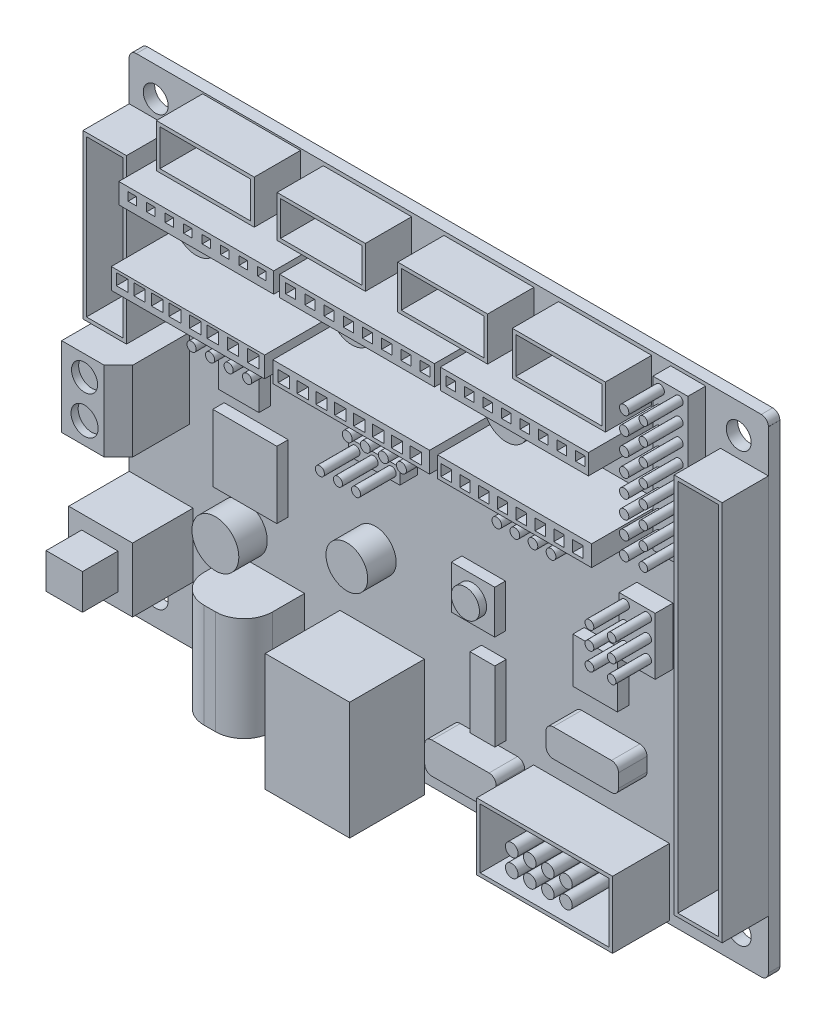
SolidWorks part; units mm, degrees
ref_plane "Plan de face" through (0, 0, 0) normal (0, 0, 1) x (1, 0, 0)
ref_plane "Plan de dessus" through (0, 0, 0) normal (0, 1, 0) x (1, 0, 0)
ref_plane "Plan de droite" through (0, 0, 0) normal (1, 0, 0) x (0, 0, -1)
sketch "Esquisse1" plane through (0, 0, 0) normal (0, 0, 1) x (1, 0, 0)
  line L0 (10.1605, 117.1315) -> (100.1605, 117.1315) construction
  line L1 (14.1823, 118.8222) -> (112.2388, 118.8222) construction
  line L2 (96.1036, 120.9113) -> (96.1036, 117.241) construction
  line L3 (14.1823, 118.8222) -> (14.1823, 52.8789) construction
  line L4 (14.1823, 58.5882) -> (96.1036, 58.5882) construction
  line L5 (17.4191, 122.975) -> (9.0854, 122.975) construction
  line L6 (10.4529, 118.3065) -> (10.4529, 124.6287) construction
  line L7 (100.2754, 62.2127) -> (100.2754, 51.8116) construction
  line L8 (93.0262, 54.5082) -> (103.9351, 54.5082) construction
  line L10 (99.2754, 54.5082) -> (11.4529, 54.5082)
  line L11 (100.2754, 55.5082) -> (100.2754, 121.975)
  line L12 (99.2754, 122.975) -> (11.4529, 122.975)
  line L13 (10.4529, 55.5082) -> (10.4529, 121.975)
  circle A0 centre (14.1823, 118.8222) radius 1.75
  circle A1 centre (96.1036, 118.8222) radius 1.75
  circle A2 centre (14.1823, 58.5882) radius 1.75
  circle A3 centre (96.1036, 58.5882) radius 1.75
  arc A4 (11.4529, 54.5082) -> (10.4529, 55.5082) centre (11.4529, 55.5082) cw
  arc A5 (99.2754, 54.5082) -> (100.2754, 55.5082) centre (99.2754, 55.5082) ccw
  arc A6 (100.2754, 121.975) -> (99.2754, 122.975) centre (99.2754, 121.975) ccw
  arc A7 (11.4529, 122.975) -> (10.4529, 121.975) centre (11.4529, 121.975) ccw
  point P30 (100.2754, 54.5082)
  point P35 (10.4529, 122.975)
  dimension "D2" = 3.5
  dimension "D3" = 1
  dimension "D1" = 90
sketch "usbplug" plane through (0, 0, 0) normal (0, 0, 1) x (1, 0, 0)
  line L1 (40.0653, 69.5241) -> (51.931, 69.5241)
  line L2 (40.0653, 69.5241) -> (40.0653, 52.9888)
  line L3 (40.0653, 52.9888) -> (51.931, 52.9888)
  line L4 (51.931, 69.5241) -> (51.931, 52.9888)
sketch "power12v" plane through (0, 0, 0) normal (0, 0, 1) x (1, 0, 0)
  line L0 (99.2754, 54.5082) -> (11.4529, 54.5082) construction
  line L1 (25.4676, 69.1019) -> (35.0978, 69.1019)
  line L2 (25.4676, 69.1019) -> (25.4676, 54.5082)
  line L3 (25.4676, 54.5082) -> (35.0978, 54.5082)
  line L4 (35.0978, 69.1019) -> (35.0978, 54.5082)
sketch "yellow females" plane through (0, 0, 0) normal (0, 0, 1) x (1, 0, 0)
  line L0 (10.4529, 55.5082) -> (10.4529, 121.975) construction
  line L1 (20.7708, 122.7288) -> (34.5297, 122.7288)
  line L2 (20.7708, 122.7288) -> (20.7708, 116.6246)
  line L3 (20.7708, 116.6246) -> (34.5297, 116.6246)
  line L4 (34.5297, 122.7288) -> (34.5297, 116.6246)
  line L5 (37.7295, 122.458) -> (50.1346, 122.458)
  line L6 (37.7295, 122.458) -> (37.7295, 116.6246)
  line L7 (37.7295, 116.6246) -> (50.1346, 116.6246)
  line L8 (50.1346, 122.458) -> (50.1346, 116.6246)
  line L9 (54.6881, 122.458) -> (67.3148, 122.458)
  line L10 (54.6881, 122.458) -> (54.6881, 116.3613)
  line L11 (54.6881, 116.3613) -> (67.3148, 116.3613)
  line L12 (67.3148, 122.458) -> (67.3148, 116.3613)
  line L13 (70.7848, 122.458) -> (83.8646, 122.458)
  line L14 (70.7848, 122.458) -> (70.7848, 116.3613)
  line L15 (70.7848, 116.3613) -> (83.8646, 116.3613)
  line L16 (83.8646, 122.458) -> (83.8646, 116.3613)
  line L17 (16.5724, 116.3613) -> (10.4529, 116.3613)
  line L18 (16.5724, 116.3613) -> (16.5724, 93.4197)
  line L19 (16.5724, 93.4197) -> (10.4529, 93.4197)
  line L20 (10.4529, 116.3613) -> (10.4529, 93.4197)
  line L21 (100.2754, 55.5082) -> (100.2754, 121.975) construction
  line L22 (100.2754, 115.984) -> (93.5394, 115.984)
  line L23 (100.2754, 115.984) -> (100.2754, 62.4145)
  line L24 (100.2754, 62.4145) -> (93.5394, 62.4145)
  line L25 (93.5394, 115.984) -> (93.5394, 62.4145)
sketch "blue connector" plane through (0, 0, 0) normal (0, 0, 1) x (1, 0, 0)
  line L1 (18.9435, 92.796) -> (10.9645, 92.796)
  line L2 (18.9435, 92.796) -> (18.9435, 81.6185)
  line L3 (18.9435, 81.6185) -> (10.9645, 81.6185)
  line L4 (10.9645, 92.796) -> (10.9645, 81.6185)
sketch "blackheaders" plane through (0, 0, 0) normal (0, 0, 1) x (1, 0, 0)
  line L1 (67.2811, 64.3182) -> (86.3744, 64.3182)
  line L2 (67.2811, 64.3182) -> (67.2811, 54.9334)
  line L3 (67.2811, 54.9334) -> (86.3744, 54.9334)
  line L4 (86.3744, 64.3182) -> (86.3744, 54.9334)
sketch "yellow males" plane through (0, 0, 0) normal (0, 0, 1) x (1, 0, 0)
  line L1 (86.5421, 122.5145) -> (91.457, 122.5145)
  line L2 (86.5421, 122.5145) -> (86.5421, 101.3571)
  line L3 (86.5421, 101.3571) -> (91.457, 101.3571)
  line L4 (91.457, 122.5145) -> (91.457, 101.3571)
  line L5 (81.7885, 93.8085) -> (86.8611, 93.8085)
  line L6 (81.7885, 93.8085) -> (81.7885, 85.7708)
  line L7 (81.7885, 85.7708) -> (86.8611, 85.7708)
  line L8 (86.8611, 93.8085) -> (86.8611, 85.7708)
  line L9 (25.6843, 99.9383) -> (35.7056, 99.9383)
  line L10 (25.6843, 99.9383) -> (25.6843, 97.555)
  line L11 (25.6843, 97.555) -> (35.7056, 97.555)
  line L12 (35.7056, 99.9383) -> (35.7056, 97.555)
  line L13 (47.4499, 99.9383) -> (57.2554, 99.9383)
  line L14 (47.4499, 99.9383) -> (47.4499, 97.555)
  line L15 (47.4499, 97.555) -> (57.2554, 97.555)
  line L16 (57.2554, 99.9383) -> (57.2554, 97.555)
  line L17 (68.6129, 99.9383) -> (78.5026, 99.9383)
  line L18 (68.6129, 99.9383) -> (68.6129, 97.555)
  line L19 (68.6129, 97.555) -> (78.5026, 97.555)
  line L20 (78.5026, 99.9383) -> (78.5026, 97.555)
  line L21 (43.7893, 93.6501) -> (50.9757, 93.6501)
  line L22 (43.7893, 93.6501) -> (43.7893, 91.4595)
  line L23 (43.7893, 91.4595) -> (50.9757, 91.4595)
  line L24 (50.9757, 93.6501) -> (50.9757, 91.4595)
sketch "capa-crystals" plane through (0, 0, 0) normal (0, 0, 1) x (1, 0, 0)
  line L1 (74.0299, 74.3373) -> (82.2137, 74.3373)
  line L2 (73.0299, 73.3373) -> (73.0299, 71.4305)
  line L3 (74.0299, 70.4305) -> (82.2137, 70.4305)
  line L4 (83.2137, 73.3373) -> (83.2137, 71.4305)
  line L5 (56.9766, 64.2091) -> (65.0123, 64.2091)
  line L6 (55.9766, 63.2091) -> (55.9766, 60.8023)
  line L7 (56.9766, 59.8023) -> (65.0123, 59.8023)
  line L8 (66.0123, 63.2091) -> (66.0123, 60.8023)
  circle A0 centre (23.8645, 109.7983) radius 3.1857
  circle A1 centre (45.7317, 109.7645) radius 3.1076
  circle A2 centre (67.4261, 108.8502) radius 3.1456
  circle A3 centre (45.0345, 79.3108) radius 2.9321
  circle A4 centre (26.5615, 72.8809) radius 3.2963
  arc A5 (56.9766, 64.2091) -> (55.9766, 63.2091) centre (56.9766, 63.2091) ccw
  arc A6 (55.9766, 60.8023) -> (56.9766, 59.8023) centre (56.9766, 60.8023) ccw
  arc A7 (65.0123, 59.8023) -> (66.0123, 60.8023) centre (65.0123, 60.8023) ccw
  arc A8 (65.0123, 64.2091) -> (66.0123, 63.2091) centre (65.0123, 63.2091) cw
  arc A9 (74.0299, 74.3373) -> (73.0299, 73.3373) centre (74.0299, 73.3373) ccw
  arc A10 (73.0299, 71.4305) -> (74.0299, 70.4305) centre (74.0299, 71.4305) ccw
  arc A11 (82.2137, 70.4305) -> (83.2137, 71.4305) centre (82.2137, 71.4305) ccw
  arc A12 (82.2137, 74.3373) -> (83.2137, 73.3373) centre (82.2137, 73.3373) cw
  dimension "D1" = 1
sketch "black smd" plane through (0, 0, 0) normal (0, 0, 1) x (1, 0, 0)
  line L1 (24.6181, 95.8453) -> (30.2856, 95.8453)
  line L2 (24.6181, 95.8453) -> (24.6181, 89.4922)
  line L3 (24.6181, 89.4922) -> (30.2856, 89.4922)
  line L4 (30.2856, 95.8453) -> (30.2856, 89.4922)
  line L5 (23.7954, 86.6584) -> (32.7994, 86.6584)
  line L6 (23.7954, 86.6584) -> (23.7954, 77.243)
  line L7 (23.7954, 77.243) -> (32.7994, 77.243)
  line L8 (32.7994, 86.6584) -> (32.7994, 77.243)
  line L9 (74.3918, 84.6016) -> (80.6535, 84.6016)
  line L10 (74.3918, 84.6016) -> (74.3918, 78.2485)
  line L11 (74.3918, 78.2485) -> (80.6535, 78.2485)
  line L12 (80.6535, 84.6016) -> (80.6535, 78.2485)
  line L13 (59.9487, 75.2319) -> (63.4224, 75.2319)
  line L14 (59.9487, 75.2319) -> (59.9487, 65.3595)
  line L15 (59.9487, 65.3595) -> (63.4224, 65.3595)
  line L16 (63.4224, 75.2319) -> (63.4224, 65.3595)
extrude "Boss.-Extru.2" add sketch "black smd" along normal blind 1.6
extrude "Boss.-Extru.3" add sketch "capa-crystals" along normal blind 4 separate body
extrude "Boss.-Extru.4" add sketch "yellow males" along normal blind 2.5 separate body
extrude "Boss.-Extru.5" add sketch "blackheaders" along normal blind 8 separate body
extrude "Boss.-Extru.6" add sketch "blue connector" along normal blind 10 separate body
extrude "Boss.-Extru.7" add sketch "yellow females" along normal blind 6.5 separate body
extrude "Boss.-Extru.8" add sketch "power12v" along normal blind 8.5 separate body
extrude "Boss.-Extru.9" add sketch "usbplug" along normal blind 10.5 separate body
sketch "button" plane through (0, 0, 0) normal (0, 0, 1) x (1, 0, 0)
  line L0 (10.4529, 55.5082) -> (10.4529, 121.975) construction
  line L1 (10.4529, 71.6421) -> (19.4201, 71.6421)
  line L2 (10.4529, 71.6421) -> (10.4529, 62.6357)
  line L3 (10.4529, 62.6357) -> (19.4201, 62.6357)
  line L4 (19.4201, 71.6421) -> (19.4201, 62.6357)
extrude "Boss.-Extru.10" add sketch "button" along normal blind 8.5 separate body
sketch "reset" plane through (0, 0, 0) normal (0, 0, 1) x (1, 0, 0)
  line L1 (57.21, 84.7172) -> (63.3186, 84.7172)
  line L2 (57.21, 84.7172) -> (57.21, 78.6371)
  line L3 (57.21, 78.6371) -> (63.3186, 78.6371)
  line L4 (63.3186, 84.7172) -> (63.3186, 78.6371)
extrude "Boss.-Extru.11" add sketch "reset" along normal blind 1.5 separate body
sketch "boutrouge" plane through (0, 0, 1.5) normal (0, 0, 1) x (1, 0, 0)
  circle A0 centre (60.1919, 81.7159) radius 1.9818
extrude "Boss.-Extru.12" add sketch "boutrouge" along normal blind 1
sketch "boutonon" plane through (0, 0, 8.5) normal (0, 0, 1) x (1, 0, 0)
  line L1 (12.2781, 69.6518) -> (17.3868, 69.6518)
  line L2 (12.2781, 69.6518) -> (12.2781, 64.69)
  line L3 (12.2781, 64.69) -> (17.3868, 64.69)
  line L4 (17.3868, 69.6518) -> (17.3868, 64.69)
extrude "Boss.-Extru.13" add sketch "boutonon" along normal blind 5
chamfer "Chanfrein1" distance 2 angle 45 1 edges at (18.9435, 87.2073, 10)
fillet "Congé1" radius 4 2 edges at (35.0978, 61.8051, 8.5) (25.4676, 61.8051, 8.5)
sketch "Esquisse14" plane through (0, 54.5082, 0) normal (0, -1, 0) x (1, 0, 0)
  circle A0 centre (30.3404, 4.6082) radius 2.8723
extrude "Enlèv. mat.-Extru.1" cut sketch "Esquisse14" against normal blind 10
sketch "Esquisse15" plane through (0, 52.9888, 0) normal (0, -1, 0) x (1, 0, 0)
  line L0 (43.6813, 8.0587) -> (48.2181, 8.0587)
  line L1 (48.2181, 8.0587) -> (50.5333, 6.3037)
  line L2 (50.5333, 6.3037) -> (50.5333, 1.7855)
  line L3 (50.5333, 1.7855) -> (41.6835, 1.7855)
  line L4 (41.6835, 1.7855) -> (41.6835, 6.3783)
  line L5 (41.6835, 6.3783) -> (43.6813, 8.0587)
  line L6 (43.6813, 6.3783) -> (48.2181, 6.3783)
  line L7 (48.2181, 6.3783) -> (48.2181, 3.5413)
  line L8 (48.2181, 3.5413) -> (43.6813, 3.5413)
  line L9 (43.6813, 3.5413) -> (43.6813, 6.3783)
extrude "Enlèv. mat.-Extru.2" cut sketch "Esquisse15" against normal blind 10
shell "Coque1" thickness 0.5
shell "Coque2" thickness 0.5
shell "Coque3" thickness 0.5
shell "Coque4" thickness 0.5
shell "Coque5" thickness 0.5
shell "Coque6" thickness 0.5
shell "Coque7" thickness 0.5
sketch "Esquisse16" plane through (0, 0, 10) normal (0, 0, 1) x (1, 0, 0)
  line L0 (14.1823, 118.8222) -> (14.1823, 52.8789) construction
  circle A0 centre (14.1823, 89.9453) radius 1.8322
  circle A1 centre (14.1823, 84.6571) radius 1.9022
extrude "Enlèv. mat.-Extru.3" cut sketch "Esquisse16" against normal blind 1
sketch "connectures jaunes" plane through (0, 0, 0) normal (0, 0, 1) x (1, 0, 0)
  line L0 (22.9016, 115.5914) -> (22.9016, 114.431)
  line L1 (18.9914, 116.1815) -> (40.7575, 116.1815)
  line L2 (18.9914, 116.1815) -> (18.9914, 113.3359)
  line L3 (18.9914, 113.3359) -> (40.7575, 113.3359)
  line L4 (40.7575, 116.1815) -> (40.7575, 113.3359)
  line L5 (41.5914, 113.3359) -> (63.3426, 113.3359)
  line L6 (41.5914, 113.3359) -> (41.5914, 116.1815)
  line L7 (41.5914, 116.1815) -> (63.3426, 116.1815)
  line L8 (63.3426, 113.3359) -> (63.3426, 116.1815)
  line L9 (64.1704, 116.1815) -> (84.9797, 116.1815)
  line L10 (64.1704, 116.1815) -> (64.1704, 113.3359)
  line L11 (64.1704, 113.3359) -> (84.9797, 113.3359)
  line L12 (84.9797, 116.1815) -> (84.9797, 113.3359)
  line L13 (20.3016, 115.5914) -> (21.4462, 115.5914)
  line L14 (20.3016, 115.5914) -> (20.3016, 114.431)
  line L15 (20.3016, 114.431) -> (21.4462, 114.431)
  line L16 (21.4462, 115.5914) -> (21.4462, 114.431)
  line L17 (22.9016, 115.5914) -> (24.0462, 115.5914)
  line L18 (24.0462, 115.5914) -> (24.0462, 114.431)
  line L19 (22.9016, 114.431) -> (24.0462, 114.431)
  line L20 (25.5016, 115.5914) -> (25.5016, 114.431)
  line L21 (25.5016, 115.5914) -> (26.6462, 115.5914)
  line L22 (26.6462, 115.5914) -> (26.6462, 114.431)
  line L23 (25.5016, 114.431) -> (26.6462, 114.431)
  line L24 (28.1016, 115.5914) -> (28.1016, 114.431)
  line L25 (28.1016, 115.5914) -> (29.2462, 115.5914)
  line L26 (29.2462, 115.5914) -> (29.2462, 114.431)
  line L27 (28.1016, 114.431) -> (29.2462, 114.431)
  line L28 (30.7016, 115.5914) -> (30.7016, 114.431)
  line L29 (30.7016, 115.5914) -> (31.8462, 115.5914)
  line L30 (31.8462, 115.5914) -> (31.8462, 114.431)
  line L31 (30.7016, 114.431) -> (31.8462, 114.431)
  line L32 (33.3016, 115.5914) -> (33.3016, 114.431)
  line L33 (33.3016, 115.5914) -> (34.4462, 115.5914)
  line L34 (34.4462, 115.5914) -> (34.4462, 114.431)
  line L35 (33.3016, 114.431) -> (34.4462, 114.431)
  line L36 (35.9016, 115.5914) -> (35.9016, 114.431)
  line L37 (35.9016, 115.5914) -> (37.0462, 115.5914)
  line L38 (37.0462, 115.5914) -> (37.0462, 114.431)
  line L39 (35.9016, 114.431) -> (37.0462, 114.431)
  line L40 (38.5016, 115.5914) -> (38.5016, 114.431)
  line L41 (38.5016, 115.5914) -> (39.6462, 115.5914)
  line L42 (39.6462, 115.5914) -> (39.6462, 114.431)
  line L43 (38.5016, 114.431) -> (39.6462, 114.431)
  line L44 (45.1347, 115.5914) -> (45.1347, 114.2232)
  line L45 (42.4347, 115.5914) -> (43.8469, 115.5914)
  line L46 (42.4347, 115.5914) -> (42.4347, 114.2232)
  line L47 (42.4347, 114.2232) -> (43.8469, 114.2232)
  line L48 (43.8469, 115.5914) -> (43.8469, 114.2232)
  line L49 (45.1347, 115.5914) -> (46.5469, 115.5914)
  line L50 (46.5469, 115.5914) -> (46.5469, 114.2232)
  line L51 (45.1347, 114.2232) -> (46.5469, 114.2232)
  line L52 (47.8347, 115.5914) -> (47.8347, 114.2232)
  line L53 (47.8347, 115.5914) -> (49.2469, 115.5914)
  line L54 (49.2469, 115.5914) -> (49.2469, 114.2232)
  line L55 (47.8347, 114.2232) -> (49.2469, 114.2232)
  line L56 (50.5347, 115.5914) -> (50.5347, 114.2232)
  line L57 (50.5347, 115.5914) -> (51.9469, 115.5914)
  line L58 (51.9469, 115.5914) -> (51.9469, 114.2232)
  line L59 (50.5347, 114.2232) -> (51.9469, 114.2232)
  line L60 (53.2347, 115.5914) -> (53.2347, 114.2232)
  line L61 (53.2347, 115.5914) -> (54.6469, 115.5914)
  line L62 (54.6469, 115.5914) -> (54.6469, 114.2232)
  line L63 (53.2347, 114.2232) -> (54.6469, 114.2232)
  line L64 (55.9347, 115.5914) -> (55.9347, 114.2232)
  line L65 (55.9347, 115.5914) -> (57.3469, 115.5914)
  line L66 (57.3469, 115.5914) -> (57.3469, 114.2232)
  line L67 (55.9347, 114.2232) -> (57.3469, 114.2232)
  line L68 (58.6347, 115.5914) -> (58.6347, 114.2232)
  line L69 (58.6347, 115.5914) -> (60.0469, 115.5914)
  line L70 (60.0469, 115.5914) -> (60.0469, 114.2232)
  line L71 (58.6347, 114.2232) -> (60.0469, 114.2232)
  line L72 (61.3347, 115.5914) -> (61.3347, 114.2232)
  line L73 (61.3347, 115.5914) -> (62.7469, 115.5914)
  line L74 (62.7469, 115.5914) -> (62.7469, 114.2232)
  line L75 (61.3347, 114.2232) -> (62.7469, 114.2232)
  line L76 (67.5787, 115.5346) -> (67.5787, 114.2232)
  line L77 (64.9787, 115.5346) -> (66.2841, 115.5346)
  line L78 (64.9787, 115.5346) -> (64.9787, 114.2232)
  line L79 (64.9787, 114.2232) -> (66.2841, 114.2232)
  line L80 (66.2841, 115.5346) -> (66.2841, 114.2232)
  line L81 (67.5787, 115.5346) -> (68.8841, 115.5346)
  line L82 (68.8841, 115.5346) -> (68.8841, 114.2232)
  line L83 (67.5787, 114.2232) -> (68.8841, 114.2232)
  line L84 (70.1787, 115.5346) -> (70.1787, 114.2232)
  line L85 (70.1787, 115.5346) -> (71.4841, 115.5346)
  line L86 (71.4841, 115.5346) -> (71.4841, 114.2232)
  line L87 (70.1787, 114.2232) -> (71.4841, 114.2232)
  line L88 (72.7787, 115.5346) -> (72.7787, 114.2232)
  line L89 (72.7787, 115.5346) -> (74.0841, 115.5346)
  line L90 (74.0841, 115.5346) -> (74.0841, 114.2232)
  line L91 (72.7787, 114.2232) -> (74.0841, 114.2232)
  line L92 (75.3787, 115.5346) -> (75.3787, 114.2232)
  line L93 (75.3787, 115.5346) -> (76.6841, 115.5346)
  line L94 (76.6841, 115.5346) -> (76.6841, 114.2232)
  line L95 (75.3787, 114.2232) -> (76.6841, 114.2232)
  line L96 (77.9787, 115.5346) -> (77.9787, 114.2232)
  line L97 (77.9787, 115.5346) -> (79.2841, 115.5346)
  line L98 (79.2841, 115.5346) -> (79.2841, 114.2232)
  line L99 (77.9787, 114.2232) -> (79.2841, 114.2232)
  line L100 (80.5787, 115.5346) -> (80.5787, 114.2232)
  line L101 (80.5787, 115.5346) -> (81.8841, 115.5346)
  line L102 (81.8841, 115.5346) -> (81.8841, 114.2232)
  line L103 (80.5787, 114.2232) -> (81.8841, 114.2232)
  line L104 (83.1787, 115.5346) -> (83.1787, 114.2232)
  line L105 (83.1787, 115.5346) -> (84.4841, 115.5346)
  line L106 (84.4841, 115.5346) -> (84.4841, 114.2232)
  line L107 (83.1787, 114.2232) -> (84.4841, 114.2232)
  dimension "D1" = 8
  dimension "D2" = 8
  dimension "D3" = 8
extrude "Boss.-Extru.14" add sketch "connectures jaunes" along normal blind 10 separate body
sketch "connecteurs noirs" plane through (0, 0, 0) normal (0, 0, 1) x (1, 0, 0)
  line L0 (44.0349, 104.4884) -> (44.0349, 102.9062)
  line L1 (17.9355, 105.3027) -> (39.478, 105.3027)
  line L2 (17.9355, 105.3027) -> (17.9355, 102.4028)
  line L3 (17.9355, 102.4028) -> (39.478, 102.4028)
  line L4 (39.478, 105.3027) -> (39.478, 102.4028)
  line L5 (40.6412, 105.3027) -> (62.6639, 105.3027)
  line L6 (40.6412, 105.3027) -> (40.6412, 102.4028)
  line L7 (40.6412, 102.4028) -> (62.6639, 102.4028)
  line L8 (62.6639, 105.3027) -> (62.6639, 102.4028)
  line L9 (63.7884, 105.3027) -> (85.4327, 105.3027)
  line L10 (63.7884, 105.3027) -> (63.7884, 102.4028)
  line L11 (63.7884, 102.4028) -> (85.4327, 102.4028)
  line L12 (85.4327, 105.3027) -> (85.4327, 102.4028)
  line L13 (18.6479, 104.9234) -> (20.2716, 104.9234)
  line L14 (18.6479, 104.9234) -> (18.6479, 103.3158)
  line L15 (18.6479, 103.3158) -> (20.2716, 103.3158)
  line L16 (20.2716, 104.9234) -> (20.2716, 103.3158)
  line L17 (21.1117, 104.9234) -> (22.7031, 104.9234)
  line L18 (21.1117, 104.9234) -> (21.1117, 103.3158)
  line L19 (21.1117, 103.3158) -> (22.7031, 103.3158)
  line L20 (22.7031, 104.9234) -> (22.7031, 103.3158)
  line L21 (23.5836, 104.9234) -> (25.1911, 104.9234)
  line L22 (23.5836, 104.9234) -> (23.5836, 103.3158)
  line L23 (23.5836, 103.3158) -> (25.1911, 103.3158)
  line L24 (25.1911, 104.9234) -> (25.1911, 103.3158)
  line L25 (26.0407, 104.9234) -> (27.7203, 104.9234)
  line L26 (26.0407, 104.9234) -> (26.0407, 103.2787)
  line L27 (26.0407, 103.2787) -> (27.7203, 103.2787)
  line L28 (27.7203, 104.9234) -> (27.7203, 103.2787)
  line L29 (28.9305, 104.9234) -> (30.5253, 104.9234)
  line L30 (28.9305, 104.9234) -> (28.9305, 103.2787)
  line L31 (28.9305, 103.2787) -> (30.5253, 103.2787)
  line L32 (30.5253, 104.9234) -> (30.5253, 103.2787)
  line L33 (31.4075, 104.9234) -> (33.0306, 104.9234)
  line L34 (31.4075, 104.9234) -> (31.4075, 103.2787)
  line L35 (31.4075, 103.2787) -> (33.0306, 103.2787)
  line L36 (33.0306, 104.9234) -> (33.0306, 103.2787)
  line L37 (34.2559, 104.8814) -> (35.8265, 104.8814)
  line L38 (34.2559, 104.8814) -> (34.2559, 103.2787)
  line L39 (34.2559, 103.2787) -> (35.8265, 103.2787)
  line L40 (35.8265, 104.8814) -> (35.8265, 103.2787)
  line L41 (37.106, 104.9234) -> (38.7227, 104.9234)
  line L42 (37.106, 104.9234) -> (37.106, 103.2046)
  line L43 (37.106, 103.2046) -> (38.7227, 103.2046)
  line L44 (38.7227, 104.9234) -> (38.7227, 103.2046)
  line L45 (41.3849, 104.4884) -> (42.9783, 104.4884)
  line L46 (41.3849, 104.4884) -> (41.3849, 102.9062)
  line L47 (41.3849, 102.9062) -> (42.9783, 102.9062)
  line L48 (42.9783, 104.4884) -> (42.9783, 102.9062)
  line L49 (44.0349, 104.4884) -> (45.6283, 104.4884)
  line L50 (45.6283, 104.4884) -> (45.6283, 102.9062)
  line L51 (44.0349, 102.9062) -> (45.6283, 102.9062)
  line L52 (46.6849, 104.4884) -> (46.6849, 102.9062)
  line L53 (46.6849, 104.4884) -> (48.2783, 104.4884)
  line L54 (48.2783, 104.4884) -> (48.2783, 102.9062)
  line L55 (46.6849, 102.9062) -> (48.2783, 102.9062)
  line L56 (49.3349, 104.4884) -> (49.3349, 102.9062)
  line L57 (49.3349, 104.4884) -> (50.9283, 104.4884)
  line L58 (50.9283, 104.4884) -> (50.9283, 102.9062)
  line L59 (49.3349, 102.9062) -> (50.9283, 102.9062)
  line L60 (51.9849, 104.4884) -> (51.9849, 102.9062)
  line L61 (51.9849, 104.4884) -> (53.5783, 104.4884)
  line L62 (53.5783, 104.4884) -> (53.5783, 102.9062)
  line L63 (51.9849, 102.9062) -> (53.5783, 102.9062)
  line L64 (54.6349, 104.4884) -> (54.6349, 102.9062)
  line L65 (54.6349, 104.4884) -> (56.2283, 104.4884)
  line L66 (56.2283, 104.4884) -> (56.2283, 102.9062)
  line L67 (54.6349, 102.9062) -> (56.2283, 102.9062)
  line L68 (57.2849, 104.4884) -> (57.2849, 102.9062)
  line L69 (57.2849, 104.4884) -> (58.8783, 104.4884)
  line L70 (58.8783, 104.4884) -> (58.8783, 102.9062)
  line L71 (57.2849, 102.9062) -> (58.8783, 102.9062)
  line L72 (59.9349, 104.4884) -> (59.9349, 102.9062)
  line L73 (59.9349, 104.4884) -> (61.5283, 104.4884)
  line L74 (61.5283, 104.4884) -> (61.5283, 102.9062)
  line L75 (59.9349, 102.9062) -> (61.5283, 102.9062)
  line L76 (66.9095, 104.4884) -> (66.9095, 102.9062)
  line L77 (64.2695, 104.4884) -> (65.7168, 104.4884)
  line L78 (64.2695, 104.4884) -> (64.2695, 102.9062)
  line L79 (64.2695, 102.9062) -> (65.7168, 102.9062)
  line L80 (65.7168, 104.4884) -> (65.7168, 102.9062)
  line L81 (66.9095, 104.4884) -> (68.3568, 104.4884)
  line L82 (68.3568, 104.4884) -> (68.3568, 102.9062)
  line L83 (66.9095, 102.9062) -> (68.3568, 102.9062)
  line L84 (69.5495, 104.4884) -> (69.5495, 102.9062)
  line L85 (69.5495, 104.4884) -> (70.9968, 104.4884)
  line L86 (70.9968, 104.4884) -> (70.9968, 102.9062)
  line L87 (69.5495, 102.9062) -> (70.9968, 102.9062)
  line L88 (72.1895, 104.4884) -> (72.1895, 102.9062)
  line L89 (72.1895, 104.4884) -> (73.6368, 104.4884)
  line L90 (73.6368, 104.4884) -> (73.6368, 102.9062)
  line L91 (72.1895, 102.9062) -> (73.6368, 102.9062)
  line L92 (74.8295, 104.4884) -> (74.8295, 102.9062)
  line L93 (74.8295, 104.4884) -> (76.2768, 104.4884)
  line L94 (76.2768, 104.4884) -> (76.2768, 102.9062)
  line L95 (74.8295, 102.9062) -> (76.2768, 102.9062)
  line L96 (77.4695, 104.4884) -> (77.4695, 102.9062)
  line L97 (77.4695, 104.4884) -> (78.9168, 104.4884)
  line L98 (78.9168, 104.4884) -> (78.9168, 102.9062)
  line L99 (77.4695, 102.9062) -> (78.9168, 102.9062)
  line L100 (80.1095, 104.4884) -> (80.1095, 102.9062)
  line L101 (80.1095, 104.4884) -> (81.5568, 104.4884)
  line L102 (81.5568, 104.4884) -> (81.5568, 102.9062)
  line L103 (80.1095, 102.9062) -> (81.5568, 102.9062)
  line L104 (82.7495, 104.4884) -> (82.7495, 102.9062)
  line L105 (82.7495, 104.4884) -> (84.1968, 104.4884)
  line L106 (84.1968, 104.4884) -> (84.1968, 102.9062)
  line L107 (82.7495, 102.9062) -> (84.1968, 102.9062)
  dimension "D1" = 8
  dimension "D2" = 8
extrude "Boss.-Extru.15" add sketch "connecteurs noirs" along normal blind 10 separate body
sketch "male poins" plane through (0, 0, 2.5) normal (0, 0, 1) x (1, 0, 0)
  circle A0 centre (26.7195, 98.6933) radius 0.6439
  circle A1 centre (29.3195, 98.6933) radius 0.6439
  circle A2 centre (31.9195, 98.6933) radius 0.6439
  circle A3 centre (34.5195, 98.6933) radius 0.6439
  circle A4 centre (48.5868, 98.6933) radius 0.6963
  circle A5 centre (51.1268, 98.6933) radius 0.6963
  circle A6 centre (53.6668, 98.6933) radius 0.6963
  circle A7 centre (56.2068, 98.6933) radius 0.6963
  circle A8 centre (44.7449, 92.564) radius 0.6367
  circle A9 centre (47.2849, 92.564) radius 0.6367
  circle A10 centre (49.8249, 92.564) radius 0.6367
  circle A11 centre (69.6044, 98.6933) radius 0.6813
  circle A12 centre (72.1444, 98.6933) radius 0.6813
  circle A13 centre (74.6844, 98.6933) radius 0.6813
  circle A14 centre (77.2244, 98.6933) radius 0.6813
  circle A15 centre (87.4992, 121.3878) radius 0.6559
  circle A16 centre (90.1934, 121.3878) radius 0.5994
  circle A17 centre (90.1934, 118.8478) radius 0.5994
  circle A18 centre (87.4992, 118.8478) radius 0.6559
  circle A19 centre (90.1934, 116.3078) radius 0.5994
  circle A20 centre (87.4992, 116.3078) radius 0.6559
  circle A21 centre (90.1934, 113.7678) radius 0.5994
  circle A22 centre (87.4992, 113.7678) radius 0.6559
  circle A23 centre (90.1934, 111.2278) radius 0.5994
  circle A24 centre (87.4992, 111.2278) radius 0.6559
  circle A25 centre (90.1934, 108.6878) radius 0.5994
  circle A26 centre (87.4992, 108.6878) radius 0.6559
  circle A27 centre (90.1934, 106.1478) radius 0.5994
  circle A28 centre (87.4992, 106.1478) radius 0.6559
  circle A29 centre (90.1934, 103.6078) radius 0.5994
  circle A30 centre (87.4992, 103.6078) radius 0.6559
  circle A31 centre (82.621, 92.7976) radius 0.6192
  circle A32 centre (85.7404, 92.7976) radius 0.6035
  circle A33 centre (85.7404, 90.2576) radius 0.6035
  circle A34 centre (82.621, 90.2576) radius 0.6192
  circle A35 centre (85.7404, 87.7176) radius 0.6035
  circle A36 centre (82.621, 87.7176) radius 0.6192
  dimension "D1" = 4
  dimension "D2" = 4
  dimension "D3" = 3
  dimension "D4" = 4
  dimension "D5" = 8
  dimension "D6" = 3
extrude "Boss.-Extru.16" add sketch "male poins" along normal blind 5
sketch "Esquisse20" plane through (1.9914, -0.7722, 0.5) normal (0, 0, 1) x (1, 0, 0)
  circle A0 centre (70.7119, 61.7232) radius 0.8865
  circle A1 centre (73.2519, 61.7232) radius 0.8865
  circle A2 centre (75.7919, 61.7232) radius 0.8865
  circle A3 centre (78.3319, 61.7232) radius 0.8865
  circle A4 centre (73.2519, 59.1832) radius 0.8865
  circle A5 centre (75.7919, 59.1832) radius 0.8865
  circle A6 centre (78.3319, 59.1832) radius 0.8865
  circle A7 centre (70.7119, 59.1832) radius 0.8865
  dimension "D1" = 4
  dimension "D2" = 2
extrude "Boss.-Extru.17" add sketch "Esquisse20" along normal blind 8
extrude "Boss.-Extru.18" add sketch "Esquisse1" against normal blind 1.6
sketch "Esquisse21" plane through (10.4529, 0, 0) normal (-1, 0, 0) x (0, 0, 1)
  line L1 (-1.6, 121.975) -> (0, 121.975)
  line L2 (-1.6, 121.975) -> (-1.6, 55.5082)
  line L3 (-1.6, 55.5082) -> (0, 55.5082)
  line L4 (0, 121.975) -> (0, 55.5082)
extrude "Boss.-Extru.19" add sketch "Esquisse21" along normal blind 0.01
sketch "Esquisse22" plane through (100.2754, 0, 0) normal (1, 0, 0) x (0, 0, -1)
  line L1 (1.6, 55.5082) -> (0, 55.5082)
  line L2 (1.6, 55.5082) -> (1.6, 121.975)
  line L3 (1.6, 121.975) -> (0, 121.975)
  line L4 (0, 55.5082) -> (0, 121.975)
extrude "Boss.-Extru.20" add sketch "Esquisse22" along normal blind 0.01
